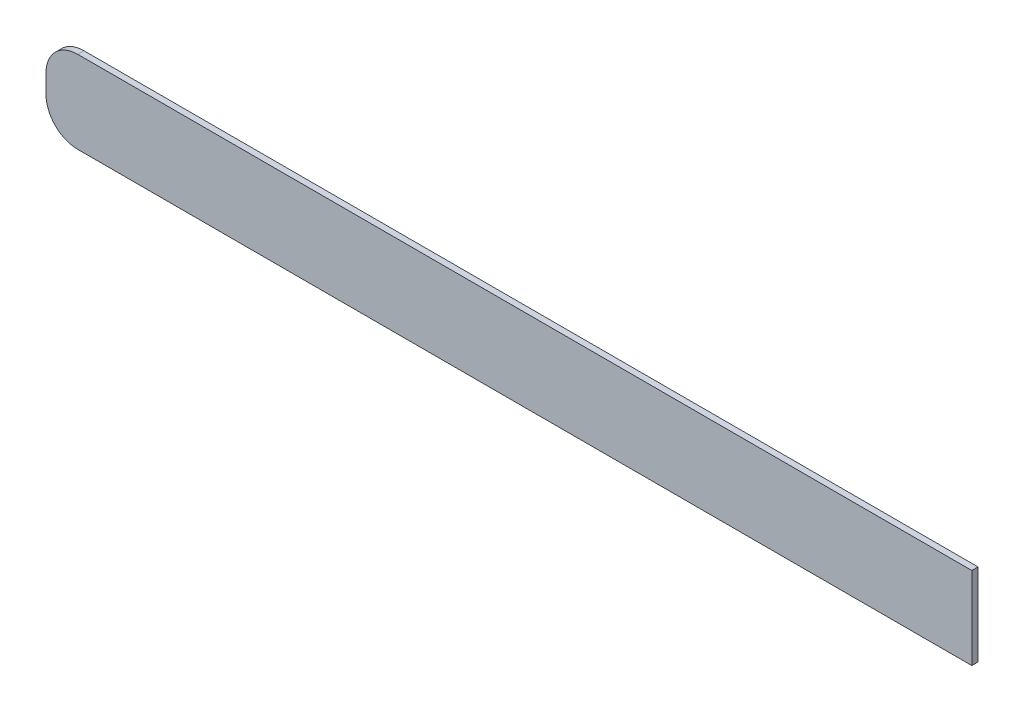
SolidWorks part; units mm, degrees
ref_plane "Front Plane" through (0, 0, 0) normal (0, 0, 1) x (1, 0, 0)
ref_plane "Top Plane" through (0, 0, 0) normal (0, 1, 0) x (1, 0, 0)
ref_plane "Right Plane" through (0, 0, 0) normal (1, 0, 0) x (0, 0, -1)
sketch "Sketch1" plane through (0, 0, 0) normal (0, 0, 1) x (1, 0, 0)
  line L1 (36.9824, -3.2893) -> (-34.4424, -3.2893)
  line L2 (36.9824, -3.2893) -> (36.9824, 3.2893)
  line L3 (36.9824, 3.2893) -> (-34.4424, 3.2893)
  line L4 (-36.9824, -0.7493) -> (-36.9824, 0.7493)
  line L5 (36.9824, -3.2893) -> (-36.9824, 3.2893) construction
  line L6 (36.9824, 3.2893) -> (-36.9824, -3.2893) construction
  arc A0 (-34.4424, 3.2893) -> (-36.9824, 0.7493) centre (-34.4424, 0.7493) ccw
  arc A1 (-34.4424, -3.2893) -> (-36.9824, -0.7493) centre (-34.4424, -0.7493) cw
  point P0 (0, 0)
  dimension "D3" = 2.54
  dimension "D1" = 6.5786
  dimension "D2" = 73.9648
extrude "Boss-Extrude1" add sketch "Sketch1" along normal blind 0.4953
